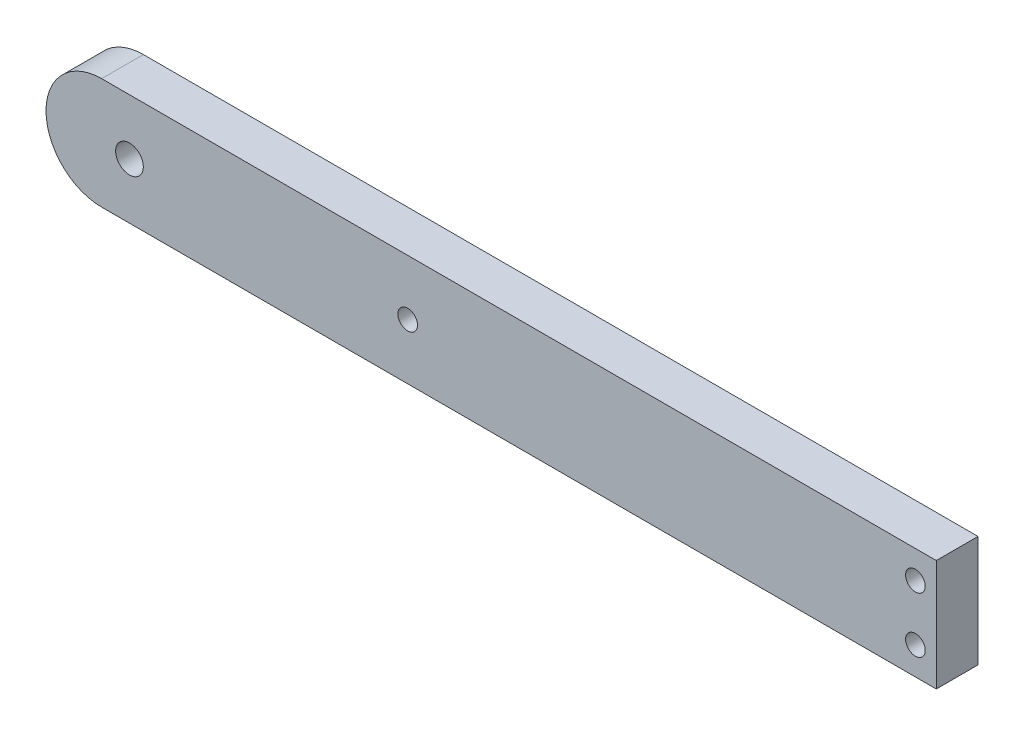
SolidWorks part; units mm, degrees
material "6061-T6 (SS)"
ref_plane "Front Plane" through (0, 0, 0) normal (0, 0, 1) x (1, 0, 0)
ref_plane "Top Plane" through (0, 0, 0) normal (0, 1, 0) x (1, 0, 0)
ref_plane "Right Plane" through (0, 0, 0) normal (1, 0, 0) x (0, 0, -1)
sketch "Sketch1" plane through (0, 0, 0) normal (0, 0, 1) x (1, 0, 0)
  line L1 (0, 0) -> (-203.2, 0)
  line L2 (0, 0) -> (0, 25.4)
  line L3 (0, 25.4) -> (-203.2, 25.4)
  line L4 (-203.2, 0) -> (-203.2, 25.4)
  dimension "D1" = 25.4
  dimension "D2" = 203.2
extrude "Boss-Extrude1" add sketch "Sketch1" along normal blind 9.525
sketch "Sketch2" plane through (0, 0, 9.525) normal (0, 0, 1) x (1, 0, 0)
  line L0 (-4.7625, 6.35) -> (-4.7625, 19.05)
  line L1 (-4.7625, 19.05) -> (-4.7625, 25.4)
  line L2 (0, 25.4) -> (-203.2, 25.4) construction
  line L3 (-4.7625, 6.35) -> (-4.7625, 0)
  line L4 (-203.2, 0) -> (0, 0) construction
  line L5 (0, 0) -> (0, 25.4) construction
  dimension "D1" = 4.7625
  dimension "D2" = 12.7
hole_wizard "#8 Clearance Hole1" positions "Sketch3" profile "Sketch4" hole size "#8" standard "ANSI Inch"
sketch "Sketch3" plane through (0, 0, 9.525) normal (0, 0, 1) x (1, 0, 0)
  point P0 (-4.7625, 6.35)
  point P3 (-4.7625, 19.05)
sketch "Sketch4" plane through (-4.7625, 6.35, 9.525) normal (1, 0, 0) x (0, -1, 0)
  line L0 (0, 0) -> (0, 26.7507)
  line L1 (0, 26.7507) -> (2.2479, 25.4)
  line L2 (2.2479, 25.4) -> (2.2479, 0)
  line L5 (2.2479, 0) -> (0, 0)
  line L10 (0, 26.7507) -> (-2.2479, 25.4) construction
  line L11 (0, -6.35) -> (0, 107.95) construction
  dimension "Hole Dia." = 4.4958
  dimension "Hole Depth" = 25.4
  dimension "Drill Angle" = 118
sketch "Sketch5" plane through (0, 0, 9.525) normal (0, 0, 1) x (1, 0, 0)
  line L0 (-203.2, 12.7) -> (-116.7098, 12.7) construction
  line L1 (-203.2, 25.4) -> (-203.2, 0) construction
  circle A0 centre (-184.15, 12.7) radius 3.1623
  point P4 (-184.15, 12.7)
  dimension "D2" = 6.3246
  dimension "D1" = 19.05
extrude "Cut-Extrude1" cut sketch "Sketch5" against normal blind 9.525 contours A0
hole_wizard "#8 Clearance Hole2" positions "Sketch8" profile "Sketch9" hole size "#8" standard "ANSI Inch"
sketch "Sketch8" plane through (0, 0, 9.525) normal (0, 0, 1) x (1, 0, 0)
  line L0 (-184.15, 12.7) -> (-120.65, 12.7)
  point P2 (-120.65, 12.7)
  dimension "D1" = 63.5
sketch "Sketch9" plane through (-120.65, 12.7, 9.525) normal (1, 0, 0) x (0, -1, 0)
  line L0 (0, 0) -> (0, 20.4007)
  line L1 (0, 20.4007) -> (2.2479, 19.05)
  line L2 (2.2479, 19.05) -> (2.2479, 0)
  line L5 (2.2479, 0) -> (0, 0)
  line L10 (0, 20.4007) -> (-2.2479, 19.05) construction
  line L11 (0, -6.35) -> (0, 107.95) construction
  dimension "Hole Dia." = 4.4958
  dimension "Hole Depth" = 19.05
  dimension "Drill Angle" = 118
sketch "Sketch10" plane through (0, 0, 9.525) normal (0, 0, 1) x (1, 0, 0)
  line L0 (-203.2, 0) -> (0, 0) construction
  line L1 (-203.2, 25.4) -> (-190.5, 25.4)
  line L2 (-203.2, 25.4) -> (-203.2, 0)
  line L3 (-203.2, 0) -> (-177.8, 0)
  arc A0 (-190.5, 0) -> (-190.5, 25.4) centre (-190.5, 12.7) cw
  point P12 (-203.2, 12.7)
  line M8 (0, 25.4) -> (-203.2, 25.4)
  line M9 (-203.2, 25.4) -> (-203.2, 0)
  line M10 (-203.2, 0) -> (0, 0)
extrude "Cut-Extrude2" cut sketch "Sketch10" against normal through all contours A0 M9 M8 | A0 L2 M10
